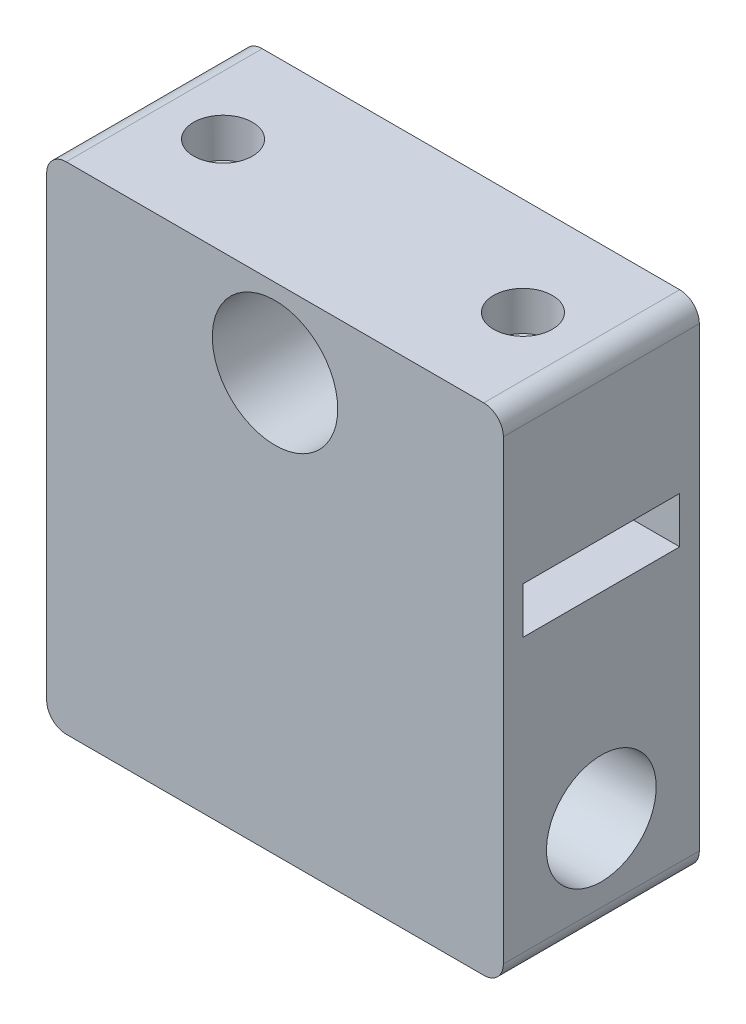
SolidWorks part; units mm, degrees
ref_plane "Front Plane" through (0, 0, 0) normal (0, 0, 1) x (1, 0, 0)
ref_plane "Top Plane" through (0, 0, 0) normal (0, 1, 0) x (1, 0, 0)
ref_plane "Right Plane" through (0, 0, 0) normal (1, 0, 0) x (0, 0, -1)
sketch "Sketch1" plane through (0, 0, 0) normal (0, 0, 1) x (1, 0, 0)
  line L1 (-14.7983, 25.4) -> (14.7983, 25.4)
  line L2 (-14.7983, 25.4) -> (-14.7983, -25.4)
  line L3 (-14.7983, -25.4) -> (14.7983, -25.4)
  line L4 (14.7983, 25.4) -> (14.7983, -25.4)
  line L5 (-14.7983, 25.4) -> (14.7983, -25.4) construction
  line L6 (-14.7983, -25.4) -> (14.7983, 25.4) construction
  circle A0 centre (0, 17.78) radius 4.064
  point P0 (0, 0)
  dimension "D1" = 8.128
  dimension "D2" = 25.4
  dimension "D3" = 7.62
extrude "Boss-Extrude1" add sketch "Sketch1" along normal blind 12.7
sketch "Sketch2" plane through (-14.7983, 0, 0) normal (-1, 0, 0) x (0, 0, 1)
  line L1 (1.27, 12.7) -> (11.43, 12.7)
  line L2 (1.27, 12.7) -> (1.27, 9.7)
  line L3 (1.27, 9.7) -> (11.43, 9.7)
  line L4 (11.43, 12.7) -> (11.43, 9.7)
  line L5 (1.27, 12.7) -> (11.43, 9.7) construction
  line L6 (1.27, 9.7) -> (11.43, 12.7) construction
  line L7 (12.7, 25.4) -> (0, 25.4) construction
  line L8 (12.7, -25.4) -> (0, -25.4) construction
  point P0 (6.35, 11.2)
  point P14 (6.35, -25.4)
  dimension "D1" = 10.16
  dimension "D2" = 3
  dimension "D3" = 12.7
extrude "Cut-Extrude1" cut sketch "Sketch2" against normal blind 30.48
sketch "Sketch3" plane through (-14.7983, 0, 0) normal (-1, 0, 0) x (0, 0, 1)
  line L0 (0, 25.4) -> (0, -25.4) construction
  line L1 (1.27, 9.7) -> (11.43, 9.7) construction
  circle A0 centre (6.35, -3) radius 3.556
  point P4 (6.35, 9.7)
  dimension "D1" = 7.112
  dimension "D2" = 6.35
  dimension "D3" = 12.7
extrude "Cut-Extrude2" cut sketch "Sketch3" against normal blind 45.72
sketch "Sketch4" plane through (0, 25.4, 0) normal (0, 1, 0) x (1, 0, 0)
  line L0 (14.7983, 0) -> (-14.7983, 0) construction
  line L1 (14.7983, -12.7) -> (14.7983, 0) construction
  line L2 (-14.7983, -12.7) -> (-14.7983, 0) construction
  circle A0 centre (9.7183, -6.35) radius 1.143
  circle A1 centre (-9.7183, -6.35) radius 1.143
  dimension "D4" = 2.286
  dimension "D5" = 2.286
  dimension "D1" = 6.35
  dimension "D2" = 5.08
  dimension "D3" = 5.08
extrude "Cut-Extrude3" cut sketch "Sketch4" against normal blind 14.2901
sketch "Sketch5" plane through (0, 25.4, 0) normal (0, 1, 0) x (1, 0, 0)
  circle A0 centre (-9.7183, -6.35) radius 1.905
  circle A1 centre (9.7183, -6.35) radius 1.905
  circle A2 centre (-9.7183, -6.35) radius 1.143 construction
  circle A3 centre (9.7183, -6.35) radius 1.143 construction
  dimension "D1" = 3.81
  dimension "D2" = 3.81
extrude "Cut-Extrude4" cut sketch "Sketch5" against normal blind 5.08
sketch "Sketch7" plane through (-14.7983, 0, 0) normal (-1, 0, 0) x (0, 0, 1)
  line L0 (0, 25.4) -> (0, -25.4) construction
  line L1 (0, -14.3495) -> (12.7, -14.3495)
  line L2 (0, -14.3495) -> (0, -25.4)
  line L3 (0, -25.4) -> (12.7, -25.4)
  line L4 (12.7, -14.3495) -> (12.7, -25.4)
extrude "Cut-Extrude5" cut sketch "Sketch7" against normal blind 62.484
sketch "Sketch8" plane through (0, 0, 12.7) normal (0, 0, 1) x (1, 0, 0)
  line L0 (-14.7983, 25.4) -> (-14.7983, -14.3495) construction
  line L1 (14.7983, 25.4) -> (-14.7983, 25.4)
  line L2 (14.7983, 25.4) -> (14.7983, 22.86)
  line L3 (14.7983, 22.86) -> (-14.7983, 22.86)
  line L4 (-14.7983, 25.4) -> (-14.7983, 22.86)
  dimension "D1" = 2.54
extrude "Cut-Extrude6" cut sketch "Sketch8" against normal blind 62.484
sketch "Sketch9" plane through (-14.7983, 0, 0) normal (-1, 0, 0) x (0, 0, 1)
  line L0 (0, 22.86) -> (0, -14.3495) construction
  line L1 (12.7, -14.3495) -> (0, -14.3495)
  line L2 (12.7, -14.3495) -> (12.7, -9.2695)
  line L3 (12.7, -9.2695) -> (0, -9.2695)
  line L4 (0, -14.3495) -> (0, -9.2695)
  dimension "D1" = 5.08
extrude "Cut-Extrude7" cut sketch "Sketch9" against normal blind 62.484
fillet "Fillet1" radius 1.27 4 edges at (-14.7983, 22.86, 6.35) (14.7983, 22.86, 6.35) (14.7983, -9.2695, 6.35) (-14.7983, -9.2695, 6.35)
